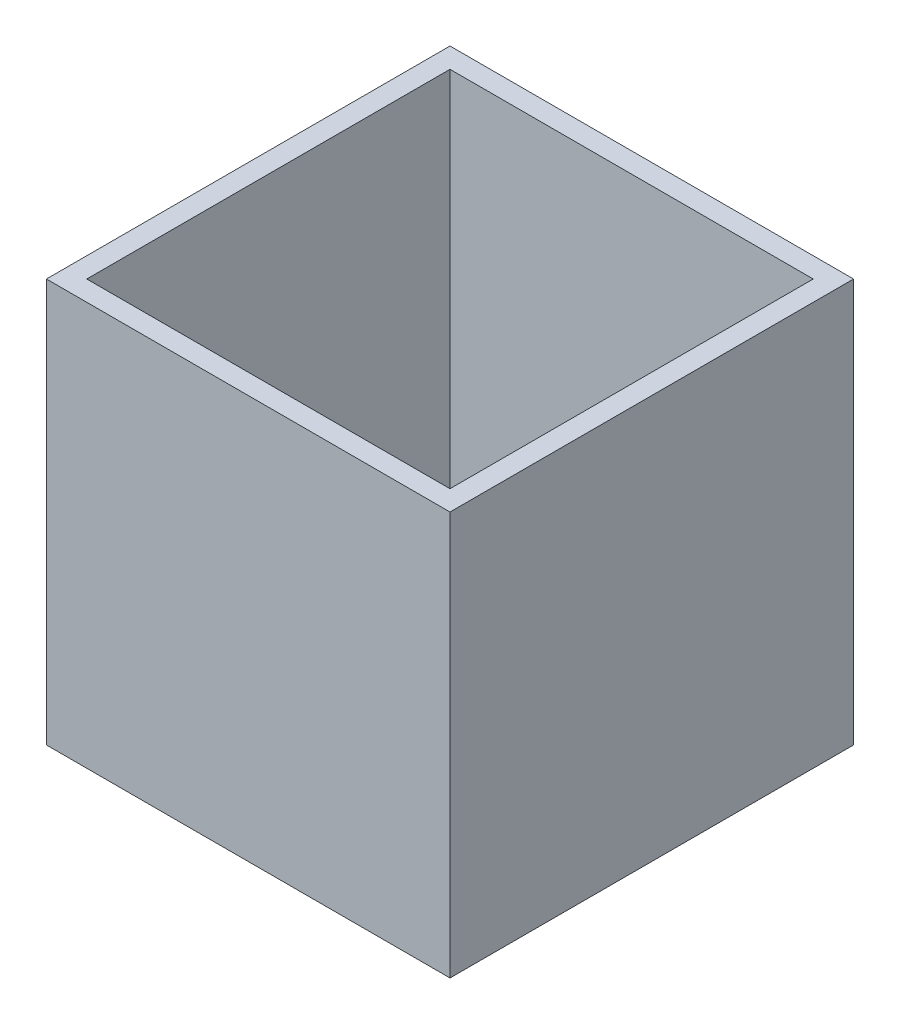
SolidWorks part; units mm, degrees
ref_plane "Front Plane" through (0, 0, 0) normal (0, 0, 1) x (1, 0, 0)
ref_plane "Top Plane" through (0, 0, 0) normal (0, 1, 0) x (1, 0, 0)
ref_plane "Right Plane" through (0, 0, 0) normal (1, 0, 0) x (0, 0, -1)
sketch "Sketch1" plane through (0, 0, 0) normal (0, 1, 0) x (1, 0, 0)
  line L1 (20, -20) -> (-20, -20)
  line L2 (20, -20) -> (20, 20)
  line L3 (20, 20) -> (-20, 20)
  line L4 (-20, -20) -> (-20, 20)
  line L5 (20, -20) -> (-20, 20) construction
  line L6 (20, 20) -> (-20, -20) construction
  point P0 (0, 0)
  dimension "D1" = 40
  dimension "D2" = 40
extrude "Extrude-Thin1" add sketch "Sketch1" along normal blind 40 thin
